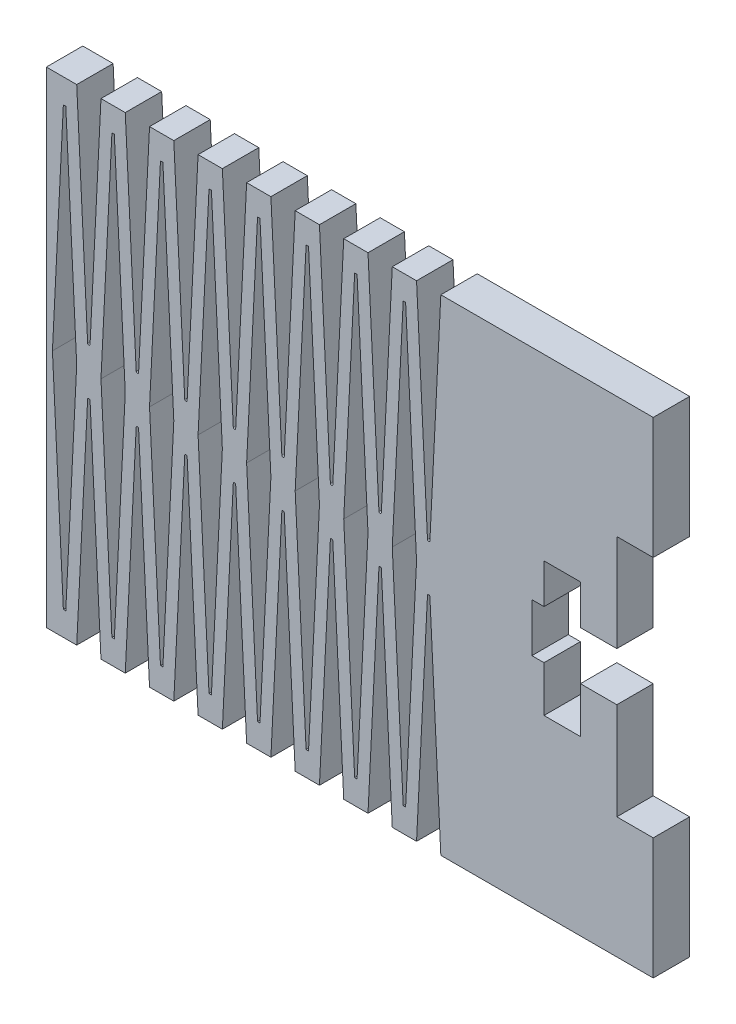
SolidWorks part; units mm, degrees
ref_plane "前视基准面" through (0, 0, 0) normal (0, 0, 1) x (1, 0, 0)
ref_plane "上视基准面" through (0, 0, 0) normal (0, 1, 0) x (1, 0, 0)
ref_plane "右视基准面" through (0, 0, 0) normal (1, 0, 0) x (0, 0, -1)
sketch "草图1" plane through (0, 0, 0) normal (0, 0, 1) x (1, 0, 0)
  line L0 (55, 0) -> (-55, 0) construction
  line L1 (-22.5, 20) -> (-25, 20)
  line L2 (-25, 20) -> (-25, -20)
  line L3 (-25, -20) -> (-22.5, -20)
  line L4 (25, 20) -> (25, 10)
  line L5 (0, -55) -> (0, 55) construction
  line L6 (16, 2) -> (15, 2)
  line L7 (7.5, 20) -> (6.5999, 1.9975)
  line L8 (6.4001, 1.9975) -> (5.5, 20)
  line L9 (40.4841, 0) -> (5.5, 0) construction
  line L10 (6.4001, -1.9975) -> (5.5, -20)
  line L11 (22, 2) -> (19, 2)
  line L12 (7.5, -20) -> (6.5999, -1.9975)
  line L13 (22, -2) -> (19, -2)
  line L14 (15, 2) -> (15, -2)
  line L15 (25, 10) -> (22, 10)
  line L16 (7.5, 20) -> (25, 20)
  line L17 (25, -10) -> (22, -10)
  line L18 (22, 10) -> (22, 2)
  line L19 (16, 5.2659) -> (19, 5.2659)
  line L20 (16, 5.2659) -> (16, 2)
  line L21 (16, -5.7697) -> (19, -5.7697)
  line L22 (19, 5.2659) -> (19, 2)
  line L23 (16, -2) -> (15, -2)
  line L24 (19, -2) -> (19, -5.7697)
  line L25 (22, -2) -> (22, -10)
  line L26 (16, -2) -> (16, -5.7697)
  line L27 (25, -10) -> (25, -20)
  line L28 (7.5, -20) -> (25, -20)
  line L29 (4.5999, 18.0025) -> (5.5, 0)
  line L30 (4.5999, -18.0025) -> (5.5, 0)
  line L31 (3.5, 0) -> (4.4001, 18.0025)
  line L32 (3.5, 0) -> (4.4001, -18.0025)
  line L33 (4.5999, 18.0025) -> (4.4001, 18.0025)
  line L34 (4.5999, -18.0025) -> (4.4001, -18.0025)
  line L35 (0.5999, -18.0025) -> (0.4001, -18.0025)
  line L36 (2.4001, -1.9975) -> (1.5, -20)
  line L37 (3.5, -20) -> (2.5999, -1.9975)
  line L38 (0.5999, -18.0025) -> (1.5, 0)
  line L39 (-0.5, 0) -> (0.4001, -18.0025)
  line L40 (-1.5999, -1.9975) -> (-2.5, -20)
  line L41 (-0.5, -20) -> (-1.4001, -1.9975)
  line L42 (0.5999, 18.0025) -> (1.5, 0)
  line L43 (-0.5, 0) -> (0.4001, 18.0025)
  line L44 (-5.5999, -1.9975) -> (-6.5, -20)
  line L45 (-4.5, -20) -> (-5.4001, -1.9975)
  line L46 (0.5999, 18.0025) -> (0.4001, 18.0025)
  line L47 (-3.4001, -18.0025) -> (-3.5999, -18.0025)
  line L48 (-9.5999, -1.9975) -> (-10.5, -20)
  line L49 (-8.5, -20) -> (-9.4001, -1.9975)
  line L50 (-3.4001, -18.0025) -> (-2.5, 0)
  line L51 (-4.5, 0) -> (-3.5999, -18.0025)
  line L52 (-13.5999, -1.9975) -> (-14.5, -20)
  line L53 (-12.5, -20) -> (-13.4001, -1.9975)
  line L54 (-3.4001, 18.0025) -> (-2.5, 0)
  line L55 (-4.5, 0) -> (-3.5999, 18.0025)
  line L56 (-17.5999, -1.9975) -> (-18.5, -20)
  line L57 (-16.5, -20) -> (-17.4001, -1.9975)
  line L58 (-3.4001, 18.0025) -> (-3.5999, 18.0025)
  line L59 (-7.4001, -18.0025) -> (-7.5999, -18.0025)
  line L60 (-21.5999, -1.9975) -> (-22.5, -20)
  line L61 (-20.5, -20) -> (-21.4001, -1.9975)
  line L62 (3.5, 20) -> (2.5999, 1.9975)
  line L63 (2.4001, 1.9975) -> (1.5, 20)
  line L64 (-7.4001, -18.0025) -> (-6.5, 0)
  line L65 (-8.5, 0) -> (-7.5999, -18.0025)
  line L66 (-0.5, 20) -> (-1.4001, 1.9975)
  line L67 (-1.5999, 1.9975) -> (-2.5, 20)
  line L68 (-7.4001, 18.0025) -> (-6.5, 0)
  line L69 (-8.5, 0) -> (-7.5999, 18.0025)
  line L70 (-4.5, 20) -> (-5.4001, 1.9975)
  line L71 (-5.5999, 1.9975) -> (-6.5, 20)
  line L72 (-7.4001, 18.0025) -> (-7.5999, 18.0025)
  line L73 (-11.4001, -18.0025) -> (-11.5999, -18.0025)
  line L74 (-8.5, 20) -> (-9.4001, 1.9975)
  line L75 (-9.5999, 1.9975) -> (-10.5, 20)
  line L76 (-11.4001, -18.0025) -> (-10.5, 0)
  line L77 (-12.5, 0) -> (-11.5999, -18.0025)
  line L78 (-12.5, 20) -> (-13.4001, 1.9975)
  line L79 (-13.5999, 1.9975) -> (-14.5, 20)
  line L80 (-11.4001, 18.0025) -> (-10.5, 0)
  line L81 (-12.5, 0) -> (-11.5999, 18.0025)
  line L82 (-16.5, 20) -> (-17.4001, 1.9975)
  line L83 (-17.5999, 1.9975) -> (-18.5, 20)
  line L84 (-11.4001, 18.0025) -> (-11.5999, 18.0025)
  line L85 (-15.4001, -18.0025) -> (-15.5999, -18.0025)
  line L86 (-20.5, 20) -> (-21.4001, 1.9975)
  line L87 (-21.5999, 1.9975) -> (-22.5, 20)
  line L88 (-15.4001, -18.0025) -> (-14.5, 0)
  line L89 (-16.5, 0) -> (-15.5999, -18.0025)
  line L90 (-4.5, 20) -> (-2.5, 20)
  line L91 (-0.5, 20) -> (1.5, 20)
  line L92 (3.5, 20) -> (5.5, 20)
  line L93 (-8.5, 20) -> (-6.5, 20)
  line L94 (-12.5, 20) -> (-10.5, 20)
  line L95 (-16.5, 20) -> (-14.5, 20)
  line L96 (-20.5, 20) -> (-18.5, 20)
  line L97 (3.5, -20) -> (5.5, -20)
  line L98 (-0.5, -20) -> (1.5, -20)
  line L99 (-4.5, -20) -> (-2.5, -20)
  line L100 (-8.5, -20) -> (-6.5, -20)
  line L101 (-12.5, -20) -> (-10.5, -20)
  line L102 (-16.5, -20) -> (-14.5, -20)
  line L103 (-20.5, -20) -> (-18.5, -20)
  line L104 (-25, 0) -> (-40.3577, 0) construction
  line L105 (-15.4001, 18.0025) -> (-14.5, 0)
  line L106 (-16.5, 0) -> (-15.5999, 18.0025)
  line L107 (-15.4001, 18.0025) -> (-15.5999, 18.0025)
  line L108 (-19.4001, -18.0025) -> (-19.5999, -18.0025)
  line L109 (-19.4001, -18.0025) -> (-18.5, 0)
  line L110 (-20.5, 0) -> (-19.5999, -18.0025)
  line L111 (-19.4001, 18.0025) -> (-18.5, 0)
  line L112 (-20.5, 0) -> (-19.5999, 18.0025)
  line L113 (-19.4001, 18.0025) -> (-19.5999, 18.0025)
  line L114 (-23.4001, -18.0025) -> (-23.5999, -18.0025)
  line L115 (-23.4001, -18.0025) -> (-22.5, 0)
  line L116 (-24.5, 0) -> (-23.5999, -18.0025)
  line L117 (-23.4001, 18.0025) -> (-22.5, 0)
  line L118 (-24.5, 0) -> (-23.5999, 18.0025)
  line L119 (-23.4001, 18.0025) -> (-23.5999, 18.0025)
  arc A0 (6.4001, 1.9975) -> (6.5999, 1.9975) centre (6.5, 2.0025) ccw
  arc A1 (6.4001, -1.9975) -> (6.5999, -1.9975) centre (6.5, -2.0025) cw
  arc A5 (2.4001, -1.9975) -> (2.5999, -1.9975) centre (2.5, -2.0025) cw
  arc A7 (-1.5999, -1.9975) -> (-1.4001, -1.9975) centre (-1.5, -2.0025) cw
  arc A9 (-5.5999, -1.9975) -> (-5.4001, -1.9975) centre (-5.5, -2.0025) cw
  arc A11 (-9.5999, -1.9975) -> (-9.4001, -1.9975) centre (-9.5, -2.0025) cw
  arc A13 (-13.5999, -1.9975) -> (-13.4001, -1.9975) centre (-13.5, -2.0025) cw
  arc A15 (-17.5999, -1.9975) -> (-17.4001, -1.9975) centre (-17.5, -2.0025) cw
  arc A17 (-21.5999, -1.9975) -> (-21.4001, -1.9975) centre (-21.5, -2.0025) cw
  arc A19 (2.4001, 1.9975) -> (2.5999, 1.9975) centre (2.5, 2.0025) ccw
  arc A20 (-1.5999, 1.9975) -> (-1.4001, 1.9975) centre (-1.5, 2.0025) ccw
  arc A21 (-5.5999, 1.9975) -> (-5.4001, 1.9975) centre (-5.5, 2.0025) ccw
  arc A22 (-9.5999, 1.9975) -> (-9.4001, 1.9975) centre (-9.5, 2.0025) ccw
  arc A23 (-13.5999, 1.9975) -> (-13.4001, 1.9975) centre (-13.5, 2.0025) ccw
  arc A24 (-17.5999, 1.9975) -> (-17.4001, 1.9975) centre (-17.5, 2.0025) ccw
  arc A25 (-21.5999, 1.9975) -> (-21.4001, 1.9975) centre (-21.5, 2.0025) ccw
  point P14 (6.5, 0)
  point P43 (4.5, 20)
  point P46 (4.5, 20)
  dimension "D15" = 0.1
  dimension "D21" = 8
  dimension "D18" = 8
  dimension "D1" = 50
  dimension "D2" = 40
  dimension "D3" = 20
  dimension "D4" = 25
  dimension "D5" = 2
  dimension "D6" = 2
  dimension "D7" = 1
  dimension "D8" = 3
  dimension "D9" = 4
  dimension "D10" = 10
  dimension "D11" = 2
  dimension "D12" = 3
  dimension "D13" = 1
  dimension "D14" = 20
  dimension "D16" = 1
  dimension "D17" = 1
  dimension "D19" = 17.5
  dimension "D22" = 8
extrude "凸台-拉伸1" add sketch "草图1" along normal mid plane 3
